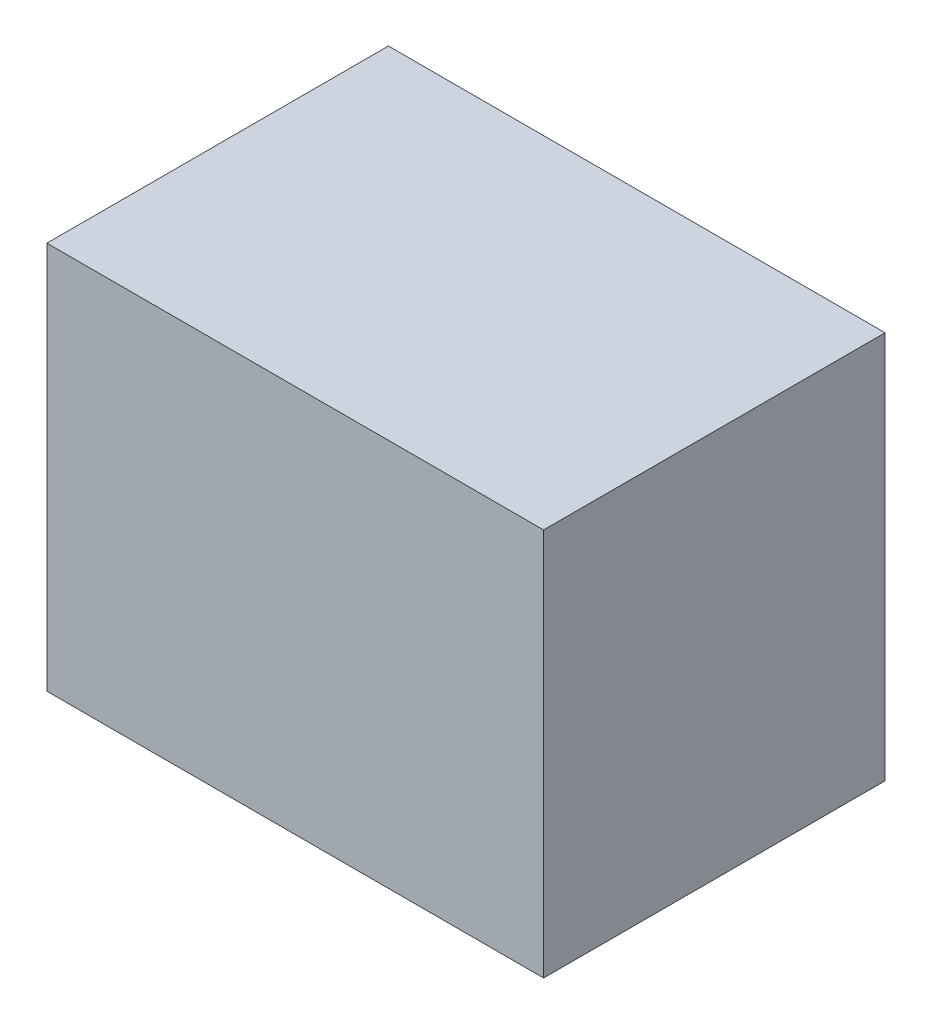
SolidWorks part; units mm, degrees
ref_plane "Front Plane" through (0, 0, 0) normal (0, 0, 1) x (1, 0, 0)
ref_plane "Top Plane" through (0, 0, 0) normal (0, 1, 0) x (1, 0, 0)
ref_plane "Right Plane" through (0, 0, 0) normal (1, 0, 0) x (0, 0, -1)
sketch "Sketch1" plane through (0, 0, 0) normal (0, 1, 0) x (1, 0, 0)
  line L1 (0, 0) -> (254, 0)
  line L2 (0, 0) -> (0, 174.625)
  line L3 (0, 174.625) -> (254, 174.625)
  line L4 (254, 0) -> (254, 174.625)
  dimension "D1" = 254
  dimension "D2" = 174.625
extrude "Boss-Extrude1" add sketch "Sketch1" along normal blind 198.4375
